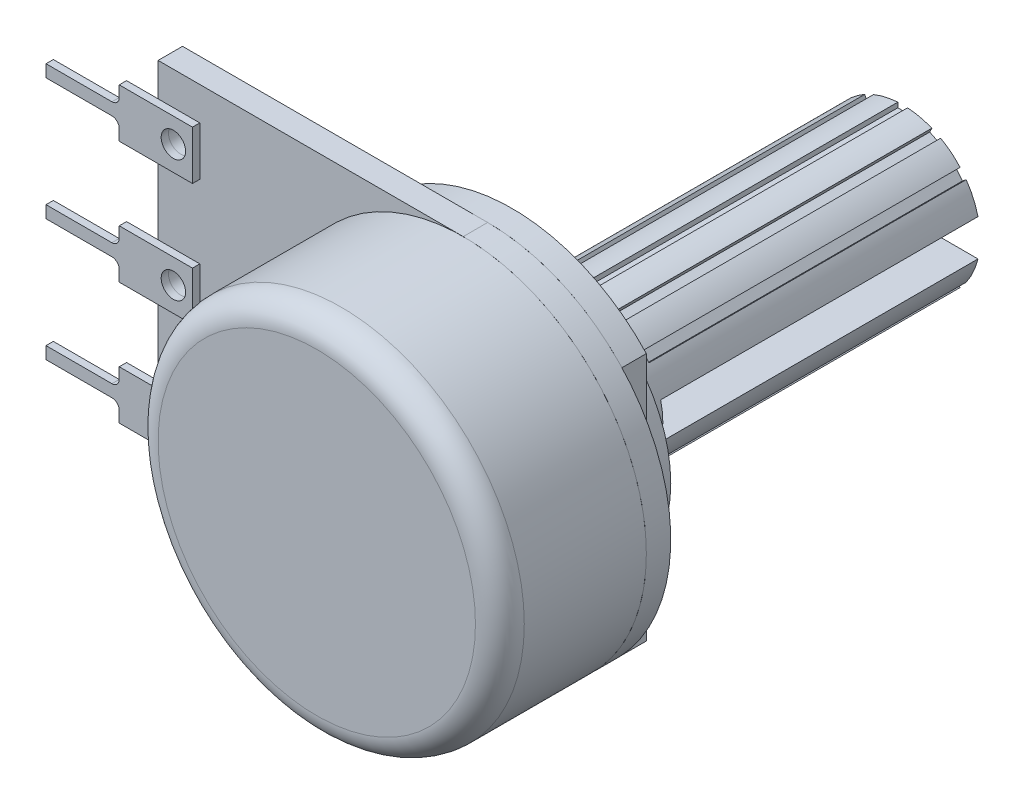
SolidWorks part; units mm, degrees
ref_plane "Alzado" through (0, 0, 0) normal (0, 0, 1) x (1, 0, 0)
ref_plane "Planta" through (0, 0, 0) normal (0, 1, 0) x (1, 0, 0)
ref_plane "Vista lateral" through (0, 0, 0) normal (1, 0, 0) x (0, 0, -1)
sketch "Croquis3" plane through (0, 0, 0) normal (0, 0, 1) x (1, 0, 0)
  line L0 (12.5, 0) -> (0, 0)
  line L1 (0, 0) -> (0, 15)
  line L2 (12.5, 15) -> (0, 15)
  arc A0 (12.5, 0) -> (12.5, 15) centre (12.5, 7.5) ccw
  point P5 (20, 7.5)
  dimension "D1" = 15
  dimension "D2" = 20
extrude "Saliente-Extruir1" add sketch "Croquis3" along normal blind 1
sketch "Croquis4" plane through (0, 0, 1) normal (0, 0, 1) x (1, 0, 0)
  circle A0 centre (12.5, 7.5) radius 7.5
  arc A1 (12.5, 0) -> (12.5, 15) centre (12.5, 7.5) ccw construction
extrude "Saliente-Extruir2" add sketch "Croquis4" along normal blind 6 separate body
sketch "Croquis5" plane through (0, 0, 0) normal (0, 0, -1) x (-1, 0, 0)
  line L0 (-12.5, 15) -> (-12.5, 0) construction
  line L1 (-18, 12.599) -> (-18, 2.401)
  line L2 (-7, 12.599) -> (-7, 2.401)
  arc A0 (-18, 2.401) -> (-7, 2.401) centre (-12.5, 7.5) ccw
  arc A1 (-12.5, 15) -> (-12.5, 0) centre (-12.5, 7.5) ccw construction
  arc A2 (-7, 12.599) -> (-18, 12.599) centre (-12.5, 7.5) ccw
  dimension "D1" = 5.5
extrude "Saliente-Extruir3" add sketch "Croquis5" along normal blind 1 separate body
sketch "Croquis6" plane through (0, 0, -1) normal (0, 0, -1) x (-1, 0, 0)
  line L2 (-12.5, 15) -> (-12.5, 0) construction
  line L4 (-18, 12.599) -> (-18, 2.401) construction
  line L6 (-7, 2.401) -> (-7, 12.599) construction
  line L7 (-18, 12.599) -> (-18, 2.401)
  line L8 (-7, 2.401) -> (-7, 12.599)
  circle A0 centre (-12.5, 7.5) radius 5.5
  arc A1 (-7, 12.599) -> (-18, 12.599) centre (-12.5, 7.5) ccw construction
  arc A2 (-7, 12.599) -> (-18, 12.599) centre (-12.5, 7.5) ccw construction
extrude "Saliente-Extruir5" add sketch "Croquis6" along normal blind 1 contours L2 A0 | A0 L2
sketch "Croquis7" plane through (0, 0, -2) normal (0, 0, -1) x (-1, 0, 0)
  circle A0 centre (-12.5, 7.5) radius 3.175
  arc A1 (-7, 7.5) -> (-18, 7.5) centre (-12.5, 7.5) ccw construction
  dimension "D1" = 6.35
extrude "Saliente-Extruir6" add sketch "Croquis7" along normal blind 15
sketch "Croquis9" plane through (0, 0, -17) normal (0, 0, -1) x (-1, 0, 0)
  line L0 (-12.5, 7.5) -> (-12.5, 10.675) construction
  line L1 (-12.7, 10.6687) -> (-12.7, 10.4687)
  line L2 (-12.7, 10.4687) -> (-12.3, 10.4687)
  line L3 (-12.3, 10.6687) -> (-12.3, 10.4687)
  line L4 (-11.3921, 10.2615) -> (-11.0317, 10.0879)
  line L5 (-11.3053, 10.4417) -> (-11.3921, 10.2615)
  line L6 (-10.945, 10.2681) -> (-11.0317, 10.0879)
  line L7 (-10.3037, 9.5073) -> (-10.0543, 9.1946)
  line L8 (-10.1473, 9.632) -> (-10.3037, 9.5073)
  line L9 (-9.8979, 9.3193) -> (-10.0543, 9.1946)
  line L10 (-9.6502, 8.3556) -> (-9.5612, 7.9656)
  line L11 (-9.4553, 8.4001) -> (-9.6502, 8.3556)
  line L12 (-9.3662, 8.0101) -> (-9.5612, 7.9656)
  line L13 (-9.5612, 7.0344) -> (-9.6502, 6.6444)
  line L14 (-9.3662, 6.9899) -> (-9.5612, 7.0344)
  line L15 (-9.4553, 6.5999) -> (-9.6502, 6.6444)
  line L16 (-10.0543, 5.8054) -> (-10.3037, 5.4927)
  line L17 (-9.8979, 5.6807) -> (-10.0543, 5.8054)
  line L18 (-10.1473, 5.368) -> (-10.3037, 5.4927)
  line L19 (-11.0317, 4.9121) -> (-11.3921, 4.7385)
  line L20 (-10.945, 4.7319) -> (-11.0317, 4.9121)
  line L21 (-11.3053, 4.5583) -> (-11.3921, 4.7385)
  line L22 (-12.3, 4.5313) -> (-12.7, 4.5313)
  line L23 (-12.3, 4.3313) -> (-12.3, 4.5313)
  line L24 (-12.7, 4.3313) -> (-12.7, 4.5313)
  line L25 (-13.6079, 4.7385) -> (-13.9683, 4.9121)
  line L26 (-13.6947, 4.5583) -> (-13.6079, 4.7385)
  line L27 (-14.055, 4.7319) -> (-13.9683, 4.9121)
  line L28 (-14.6963, 5.4927) -> (-14.9457, 5.8054)
  line L29 (-14.8527, 5.368) -> (-14.6963, 5.4927)
  line L30 (-15.1021, 5.6807) -> (-14.9457, 5.8054)
  line L31 (-15.3498, 6.6444) -> (-15.4388, 7.0344)
  line L32 (-15.5447, 6.5999) -> (-15.3498, 6.6444)
  line L33 (-15.6338, 6.9899) -> (-15.4388, 7.0344)
  line L34 (-15.4388, 7.9656) -> (-15.3498, 8.3556)
  line L35 (-15.6338, 8.0101) -> (-15.4388, 7.9656)
  line L36 (-15.5447, 8.4001) -> (-15.3498, 8.3556)
  line L37 (-14.9457, 9.1946) -> (-14.6963, 9.5073)
  line L38 (-15.1021, 9.3193) -> (-14.9457, 9.1946)
  line L39 (-14.8527, 9.632) -> (-14.6963, 9.5073)
  line L40 (-13.9683, 10.0879) -> (-13.6079, 10.2615)
  line L41 (-14.055, 10.2681) -> (-13.9683, 10.0879)
  line L42 (-13.6947, 10.4417) -> (-13.6079, 10.2615)
  line L43 (-15.675, 7.5) -> (-9.325, 7.5) construction
  line L44 (-15.5851, 8.25) -> (-9.4149, 8.25)
  line L45 (-15.5851, 6.75) -> (-9.4149, 6.75)
  circle A0 centre (-12.5, 7.5) radius 3.175
  circle A1 centre (-12.5, 7.5) radius 3.175
  circle A2 centre (-12.5, 7.5) radius 3.175
  circle A3 centre (-12.5, 7.5) radius 3.175
  circle A4 centre (-12.5, 7.5) radius 3.175
  circle A5 centre (-12.5, 7.5) radius 3.175
  circle A6 centre (-12.5, 7.5) radius 3.175
  circle A7 centre (-12.5, 7.5) radius 3.175
  circle A8 centre (-12.5, 7.5) radius 3.175
  circle A9 centre (-12.5, 7.5) radius 3.175
  circle A10 centre (-12.5, 7.5) radius 3.175
  circle A11 centre (-12.5, 7.5) radius 3.175
  circle A12 centre (-12.5, 7.5) radius 3.175
  circle A13 centre (-12.5, 7.5) radius 3.175
  circle A14 centre (-12.5, 7.5) radius 3.175
  point P9 (-12.5, 10.4687)
  point P76 (-12.5, 7.5)
  circle M2 centre (-12.5, 7.5) radius 3.175
  dimension "D2" = 0.2
  dimension "D3" = 0.2
  dimension "D5" = 0.75
  dimension "D1" = 0
  dimension "D4" = 14
extrude "Cortar-Extruir1" cut sketch "Croquis9" against normal blind 13 contours L31 L45 L13 L14 L12 L10 L44 L34 L35 L33 M2 | L39 L38 L37 M2 | L42 L41 L40 M2 | L3 L1 L2 M2 | L6 L5 L4 M2 | L9 L8 L7 M2 | L30 L29 L28 M2 | L27 L26 L25 M2 | L21 L20 L19 M2 | L24 L23 L22 M2 | L18 L17 L16 M2 | L45 L31 L33 M2 | L13 L45 L14 M2 | L44 L10 L12 M2 | L44 L35 L34 M2
sketch "Croquis10" plane through (0, 0, 1) normal (0, 0, 1) x (1, 0, 0)
  line L0 (-4.2922, 12.6362) -> (-1.2922, 12.6362) construction
  line L1 (1.7078, 13.6362) -> (-1.2922, 13.6362)
  line L2 (1.7078, 13.6362) -> (1.7078, 11.6362)
  line L3 (1.7078, 11.6362) -> (-1.2922, 11.6362)
  line L4 (-1.2922, 13.6362) -> (-1.2922, 13.1862)
  line L5 (-1.5922, 12.8862) -> (-4.2922, 12.8862)
  line L6 (1.7078, 6.6362) -> (-1.2922, 6.6362)
  line L7 (-1.5922, 12.3862) -> (-4.2922, 12.3862)
  line L8 (-4.2922, 12.8862) -> (-4.2922, 12.3862)
  line L9 (-1.2922, 12.0862) -> (-1.2922, 11.6362)
  line L10 (1.7078, 8.6362) -> (1.7078, 6.6362)
  line L11 (1.7078, 8.6362) -> (-1.2922, 8.6362)
  line L12 (-1.2922, 8.6362) -> (-1.2922, 8.1862)
  line L13 (-1.5922, 7.8862) -> (-4.2922, 7.8862)
  line L14 (-4.2922, 7.8862) -> (-4.2922, 7.3862)
  line L15 (-1.5922, 7.3862) -> (-4.2922, 7.3862)
  line L16 (1.7078, 1.6362) -> (-1.2922, 1.6362)
  line L17 (1.7078, 3.6362) -> (1.7078, 1.6362)
  line L18 (1.7078, 3.6362) -> (-1.2922, 3.6362)
  line L19 (-1.2922, 3.6362) -> (-1.2922, 3.1862)
  line L20 (-1.5922, 2.8862) -> (-4.2922, 2.8862)
  line L21 (-4.2922, 2.8862) -> (-4.2922, 2.3862)
  line L22 (-1.5922, 2.3862) -> (-4.2922, 2.3862)
  line L23 (-1.2922, 7.0862) -> (-1.2922, 6.6362)
  line L24 (-1.2922, 2.0862) -> (-1.2922, 1.6362)
  line L25 (-1.2922, 1.6362) -> (-1.3441, 1.6111)
  line L26 (12.5, 15) -> (0, 15) construction
  arc A0 (-1.2922, 12.0862) -> (-1.5922, 12.3862) centre (-1.5922, 12.0862) ccw
  arc A1 (-1.5922, 12.8862) -> (-1.2922, 13.1862) centre (-1.5922, 13.1862) ccw
  arc A2 (-1.5922, 7.8862) -> (-1.2922, 8.1862) centre (-1.5922, 8.1862) ccw
  arc A3 (-1.2922, 7.0862) -> (-1.5922, 7.3862) centre (-1.5922, 7.0862) ccw
  arc A4 (-1.5922, 2.8862) -> (-1.2922, 3.1862) centre (-1.5922, 3.1862) ccw
  arc A5 (-1.2922, 2.0862) -> (-1.5922, 2.3862) centre (-1.5922, 2.0862) ccw
  point P12 (-1.2922, 12.3862)
  dimension "D5" = 0.3
  dimension "D1" = 0.5
  dimension "D2" = 3
  dimension "D3" = 2
  dimension "D4" = 3
  dimension "D7" = 1.3638
  dimension "D6" = 3
extrude "Saliente-Extruir7" add sketch "Croquis10" along normal blind 0.3 separate body
sketch "Croquis11" plane through (0, 0, 1.3) normal (0, 0, 1) x (1, 0, 0)
  line L0 (1.7078, 13.6362) -> (1.7078, 11.6362) construction
  line L1 (1.7078, 13.6362) -> (1.7078, 11.6362)
  line L2 (1.7078, 12.6362) -> (0.9252, 12.6362) construction
  circle A0 centre (0.9252, 12.6362) radius 0.5
  circle A1 centre (0.9252, 7.6362) radius 0.5
  circle A2 centre (0.9252, 2.6362) radius 0.5
  dimension "D1" = 1
  dimension "D2" = 3
extrude "Cortar-Extruir2" cut sketch "Croquis11" against normal through all
fillet "Redondeo1" radius 1 1 edges at (20, 7.5, 7)
fillet "Redondeo2" radius 1 1 edges at (9.325, 7.5, -2)
split "Partir1" bodies to split 111 resulting bodies 115
